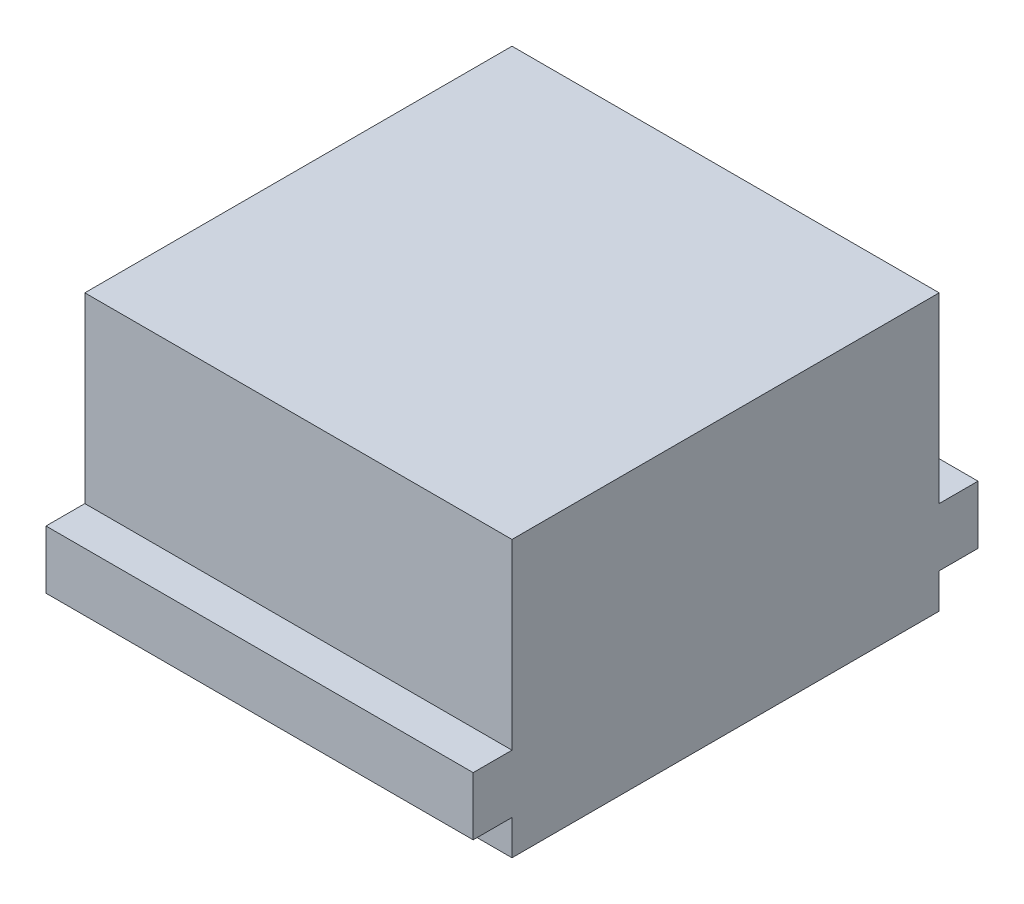
SolidWorks part; units mm, degrees
ref_plane "前视基准面" through (0, 0, 0) normal (0, 0, 1) x (1, 0, 0)
ref_plane "上视基准面" through (0, 0, 0) normal (0, 1, 0) x (1, 0, 0)
ref_plane "右视基准面" through (0, 0, 0) normal (1, 0, 0) x (0, 0, -1)
other "Configuration Table"
sketch "草图1" plane through (0, 0, 0) normal (0, 1, 0) x (1, 0, 0)
  line L1 (0, 0) -> (110, 0)
  line L2 (0, 0) -> (0, 110)
  line L3 (0, 110) -> (110, 110)
  line L4 (110, 0) -> (110, 110)
  dimension "D1" = 110
  dimension "D2" = 110
extrude "凸台-拉伸1" add sketch "草图1" along normal blind 71
sketch "草图2" plane through (0, 0, 0) normal (0, 0, 1) x (1, 0, 0)
  line L0 (0, 71) -> (0, 0) construction
  line L1 (110, 0) -> (0, 0)
  line L2 (110, 0) -> (110, 24)
  line L3 (110, 24) -> (0, 24)
  line L4 (0, 0) -> (0, 24)
  line L6 (0, 24) -> (110, 24)
  line L7 (0, 24) -> (0, 9)
  line L8 (0, 9) -> (110, 9)
  line L9 (110, 24) -> (110, 9)
  line M5 (0, 71) -> (0, 0)
  dimension "D1" = 24
  dimension "D2" = 15
extrude "凸台-拉伸3" add sketch "草图2" along normal blind 10 contours L8 L2 L3 M5
sketch "草图3" plane through (0, 0, -110) normal (0, 0, -1) x (-1, 0, 0)
  line L0 (0, 71) -> (0, 0) construction
  line L1 (-110, 0) -> (0, 0)
  line L2 (-110, 0) -> (-110, 24)
  line L3 (-110, 24) -> (0, 24)
  line L4 (0, 0) -> (0, 24)
  line L6 (-110, 24) -> (0, 24)
  line L7 (-110, 24) -> (-110, 9)
  line L8 (-110, 9) -> (0, 9)
  line L9 (0, 24) -> (0, 9)
  line M6 (-110, 71) -> (-110, 0)
  dimension "D1" = 24
  dimension "D2" = 15
extrude "凸台-拉伸4" add sketch "草图3" along normal blind 10 contours L8 L4 L3 M6
